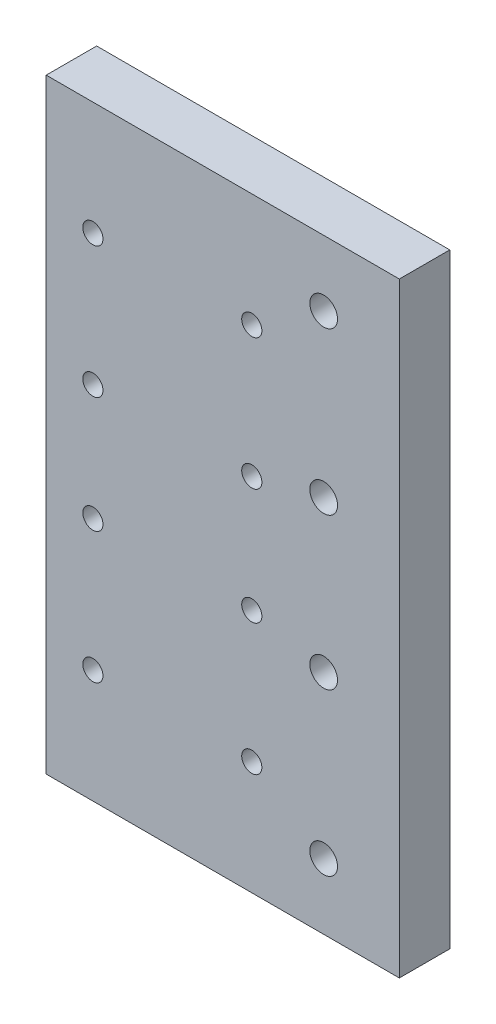
SolidWorks part; units mm, degrees
ref_plane "Ön Düzlem" through (0, 0, 0) normal (0, 0, 1) x (1, 0, 0)
ref_plane "Üst Düzlem" through (0, 0, 0) normal (0, 1, 0) x (1, 0, 0)
ref_plane "Sağ Düzlem" through (0, 0, 0) normal (1, 0, 0) x (0, 0, -1)
sketch "Sketch1" plane through (0, 0, 0) normal (0, 0, 1) x (1, 0, 0)
  line L0 (0, -60) -> (0, 60)
  line L1 (0, 60) -> (-70, 60)
  line L2 (-70, 60) -> (-70, -60)
  line L3 (-70, -60) -> (0, -60)
  line L4 (-45, 24.5) -> (-45, -24.5) construction
  line L11 (-60.75, 11.5) -> (-29.25, 11.5) construction
  line L12 (-60.75, 11.5) -> (-60.75, 37.5) construction
  line L13 (-60.75, 37.5) -> (-29.25, 37.5) construction
  line L14 (-29.25, 11.5) -> (-29.25, 37.5) construction
  line L15 (-60.75, 11.5) -> (-29.25, 37.5) construction
  line L16 (-60.75, 37.5) -> (-29.25, 11.5) construction
  line L17 (-60.75, -37.5) -> (-29.25, -37.5) construction
  line L18 (-60.75, -37.5) -> (-60.75, -11.5) construction
  line L19 (-60.75, -11.5) -> (-29.25, -11.5) construction
  line L20 (-29.25, -37.5) -> (-29.25, -11.5) construction
  line L21 (-60.75, -37.5) -> (-29.25, -11.5) construction
  line L22 (-60.75, -11.5) -> (-29.25, -37.5) construction
  line L25 (-15, 47) -> (-15, 15) construction
  line L26 (-15, -15) -> (-15, -47) construction
  line L27 (-15, 31) -> (-15, -31) construction
  circle A5 centre (-60.75, 37.5) radius 2
  circle A6 centre (-29.25, 37.5) radius 2
  circle A7 centre (-60.75, 11.5) radius 2
  circle A8 centre (-29.25, 11.5) radius 2
  circle A9 centre (-60.75, -11.5) radius 2
  circle A10 centre (-29.25, -11.5) radius 2
  circle A11 centre (-29.25, -37.5) radius 2
  circle A12 centre (-60.75, -37.5) radius 2
  circle A13 centre (-15, 47) radius 2.75
  circle A14 centre (-15, 15) radius 2.75
  circle A15 centre (-15, -15) radius 2.75
  circle A16 centre (-15, -47) radius 2.75
  point P0 (0, 0)
  point P3 (0, 0)
  point P4 (0, 0)
  point P16 (-45, -24.5)
  point P19 (-45, 24.5)
  point P29 (-45, 0)
  point P51 (-15, 0)
  dimension "D11" = 4
  dimension "D13" = 5.5
  dimension "D16" = 15
  dimension "D1" = 120
  dimension "D2" = 70
  dimension "D7" = 31.5
  dimension "D8" = 26
  dimension "D9" = 23
  dimension "D10" = 45
  dimension "D12" = 32
  dimension "D17" = 30
extrude "Boss-Extrude1" add sketch "Sketch1" along normal blind 10
